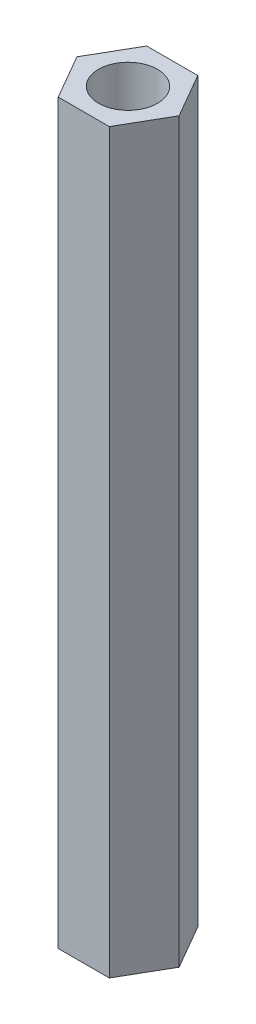
SolidWorks part; units mm, degrees
ref_plane "前视基准面" through (0, 0, 0) normal (0, 0, 1) x (1, 0, 0)
ref_plane "上视基准面" through (0, 0, 0) normal (0, 1, 0) x (1, 0, 0)
ref_plane "右视基准面" through (0, 0, 0) normal (1, 0, 0) x (0, 0, -1)
sketch "草图1" plane through (0, 0, 0) normal (0, 1, 0) x (1, 0, 0)
  line L1 (1.7321, 3) -> (-1.7321, 3)
  line L2 (-1.7321, 3) -> (-3.4641, 0)
  line L3 (-3.4641, 0) -> (-1.7321, -3)
  line L4 (-1.7321, -3) -> (1.7321, -3)
  line L5 (1.7321, -3) -> (3.4641, 0)
  line L6 (3.4641, 0) -> (1.7321, 3)
  circle A0 centre (0, 0) radius 3 construction
  circle A1 centre (0, 0) radius 2
  dimension "D1" = 6
  dimension "D2" = 4
extrude "凸台-拉伸1" add sketch "草图1" along normal blind 50
